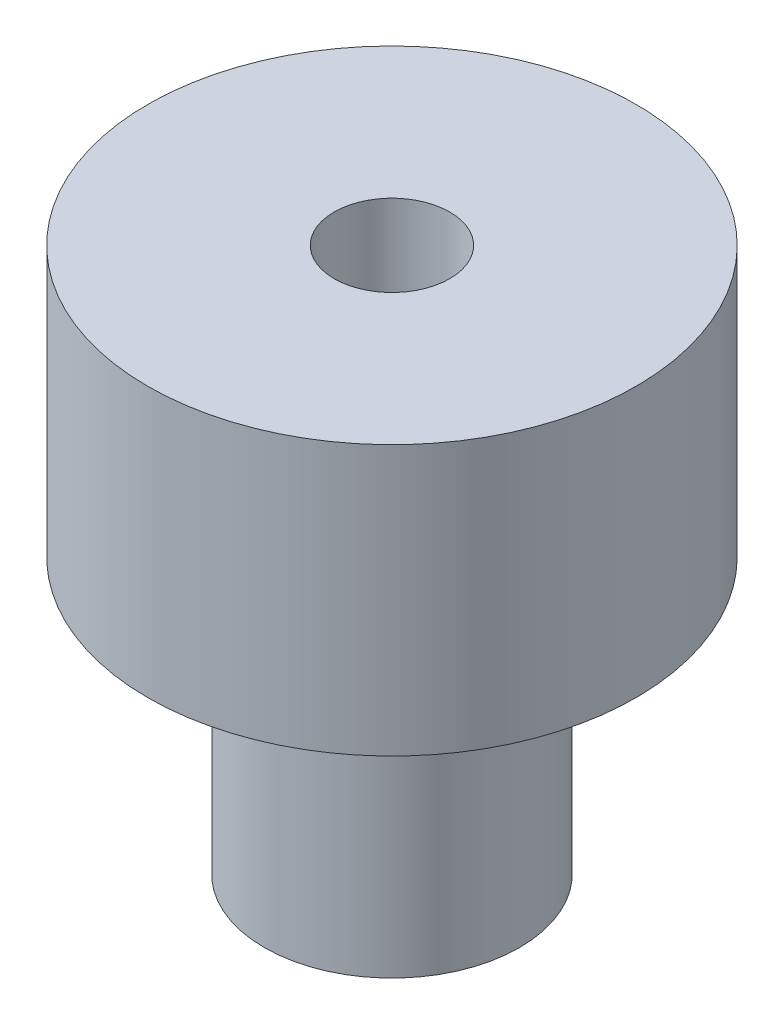
SolidWorks part; units mm, degrees
ref_plane "Front Plane" through (0, 0, 0) normal (0, 0, 1) x (1, 0, 0)
ref_plane "Top Plane" through (0, 0, 0) normal (0, 1, 0) x (1, 0, 0)
ref_plane "Right Plane" through (0, 0, 0) normal (1, 0, 0) x (0, 0, -1)
sketch "Sketch1" plane through (0, 0, 0) normal (0, 1, 0) x (1, 0, 0)
  circle A0 centre (0, 0) radius 6.7
  circle A1 centre (0, 0) radius 1.586
  dimension "D1" = 13.4
  dimension "D2" = 3.172
extrude "Boss-Extrude1" add sketch "Sketch1" along normal blind 7.4
sketch "Sketch2" plane through (0, 0, 0) normal (0, -1, 0) x (1, 0, 0)
  circle A0 centre (0, 0) radius 3.5
  circle A1 centre (0, 0) radius 1.586
  circle A2 centre (0, 0) radius 1.586 construction
  dimension "D1" = 7
extrude "Boss-Extrude2" add sketch "Sketch2" along normal blind 7.54
sketch "Sketch3" plane through (0, 0, 0) normal (1, 0, 0) x (0, 0, -1)
  line L0 (0, 0) -> (0, -7.54) construction
  line L1 (-3.5, -7.54) -> (3.5, -7.54) construction
  line L2 (-3.5, -3.77) -> (3.5, -3.77) construction
  line L3 (3.5, -7.54) -> (3.5, 0) construction
  circle A0 centre (0, -3.77) radius 1.25
  point P10 (0, -3.77)
  dimension "D1" = 2.5
extrude "Cut-Extrude1" cut sketch "Sketch3" against normal blind 10
